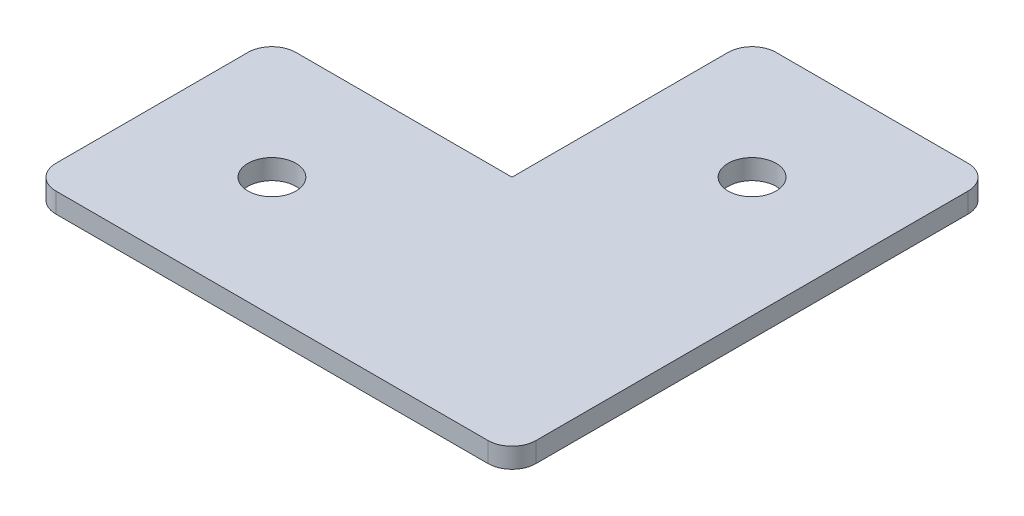
SolidWorks part; units mm, degrees
ref_plane "Front Plane" through (0, 0, 0) normal (0, 0, 1) x (1, 0, 0)
ref_plane "Top Plane" through (0, 0, 0) normal (0, 1, 0) x (1, 0, 0)
ref_plane "Right Plane" through (0, 0, 0) normal (1, 0, 0) x (0, 0, -1)
sketch "Sketch1" plane through (0, 0, 0) normal (0, 1, 0) x (1, 0, 0)
  line L1 (-12.4699, 24.8494) -> (17.5301, 24.8494)
  line L2 (-12.4699, 24.8494) -> (-12.4699, -5.1506)
  line L3 (-12.4699, -35.1506) -> (17.5301, -35.1506)
  line L4 (17.5301, 24.8494) -> (17.5301, -35.1506)
  line L5 (-12.4699, -35.1506) -> (-42.4699, -35.1506)
  line L7 (-12.4699, -5.1506) -> (-42.4699, -5.1506)
  line L8 (-42.4699, -35.1506) -> (-42.4699, -5.1506)
  dimension "D1" = 30
  dimension "D2" = 60
  dimension "D3" = 30
  dimension "D4" = 30
extrude "Boss-Extrude1" add sketch "Sketch1" along normal blind 2.5
fillet "Fillet1" radius 3 1 edges at (-42.4699, 1.25, 5.1506)
fillet "Fillet2" radius 3 1 edges at (-42.4699, 1.25, 35.1506)
fillet "Fillet3" radius 3 1 edges at (17.5301, 1.25, 35.1506)
fillet "Fillet4" radius 3 1 edges at (17.5301, 1.25, -24.8494)
fillet "Fillet5" radius 3 1 edges at (-12.4699, 1.25, -24.8494)
sketch "Sketch2" plane through (0, 2.5, 0) normal (0, 1, 0) x (1, 0, 0)
  line L0 (-12.4699, 21.8494) -> (-12.4699, -5.1506) construction
  line L1 (-39.4699, -35.1506) -> (14.5301, -35.1506) construction
  line L2 (-42.4699, -8.1506) -> (-42.4699, -32.1506) construction
  line L3 (14.5301, 24.8494) -> (-9.4699, 24.8494) construction
  circle A0 centre (2.5301, 9.8494) radius 3
  circle A1 centre (-27.4699, -20.1506) radius 3
  dimension "D1" = 15
  dimension "D2" = 15
  dimension "D3" = 15
  dimension "D4" = 15
extrude "Cut-Extrude1" cut sketch "Sketch2" against normal blind 3
